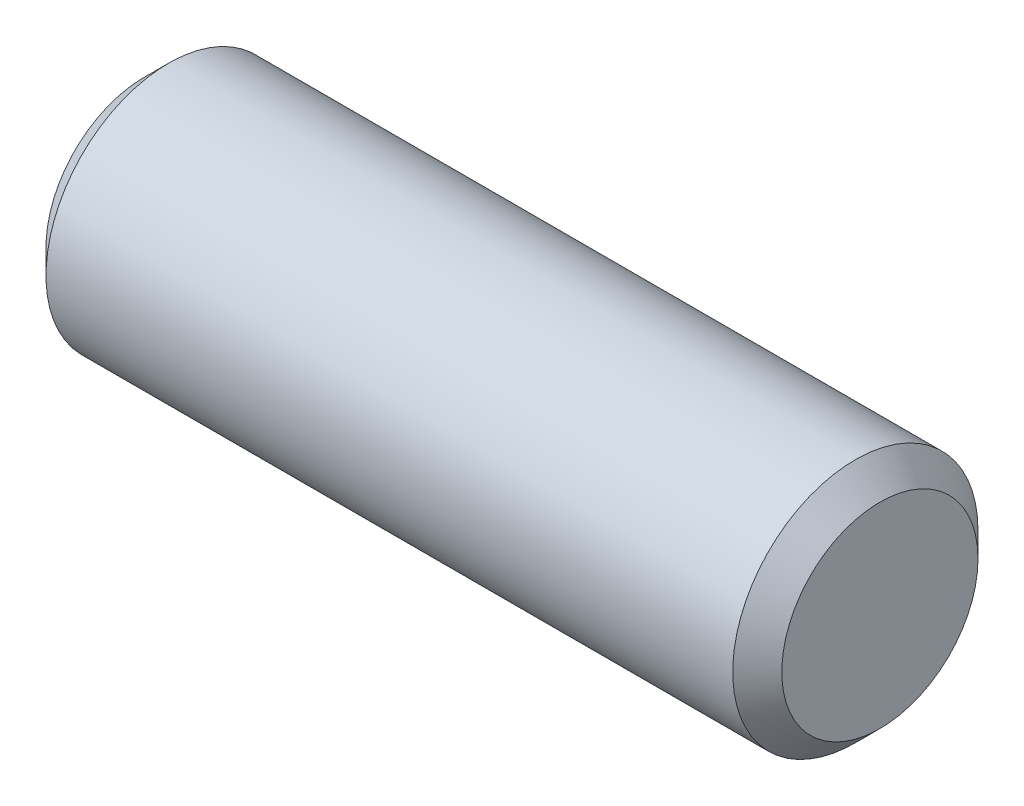
SolidWorks part; units mm, degrees
ref_plane "Front Plane" through (0, 0, 0) normal (0, 0, 1) x (1, 0, 0)
ref_plane "Top Plane" through (0, 0, 0) normal (0, 1, 0) x (1, 0, 0)
ref_plane "Right Plane" through (0, 0, 0) normal (1, 0, 0) x (0, 0, -1)
sketch "Sketch1" plane through (0, 0, 0) normal (0, 0, 1) x (1, 0, 0)
  line L0 (-4.7625, 0) -> (4.7625, 0) construction
  line L1 (-4.7625, 1.5875) -> (-4.7625, -1.5875) construction
  line L2 (4.7625, 1.5875) -> (4.7625, -1.5875) construction
  dimension "Diameter" = 3.175
  dimension "Length" = 9.525
sketch "Sketch2" plane through (0, 0, 0) normal (1, 0, 0) x (0, 0, -1)
  circle A0 centre (0, 0) radius 1.5875
extrude "Extrude1" add sketch "Sketch2" against normal up to vertex (4.7625 mm away) and the other way up to vertex (4.7625 mm away) up to point (-4.7625, 0, 0) other way up to point (4.7625, 0, 0)
chamfer "Chamfer1" distance 0.3175 angle 45 2 edges at (4.7625, 0, -1.5875) (-4.7625, 0, -1.5875)
equation "\"D1@Chamfer1\" = \"Diameter@Sketch1\"*.1"
